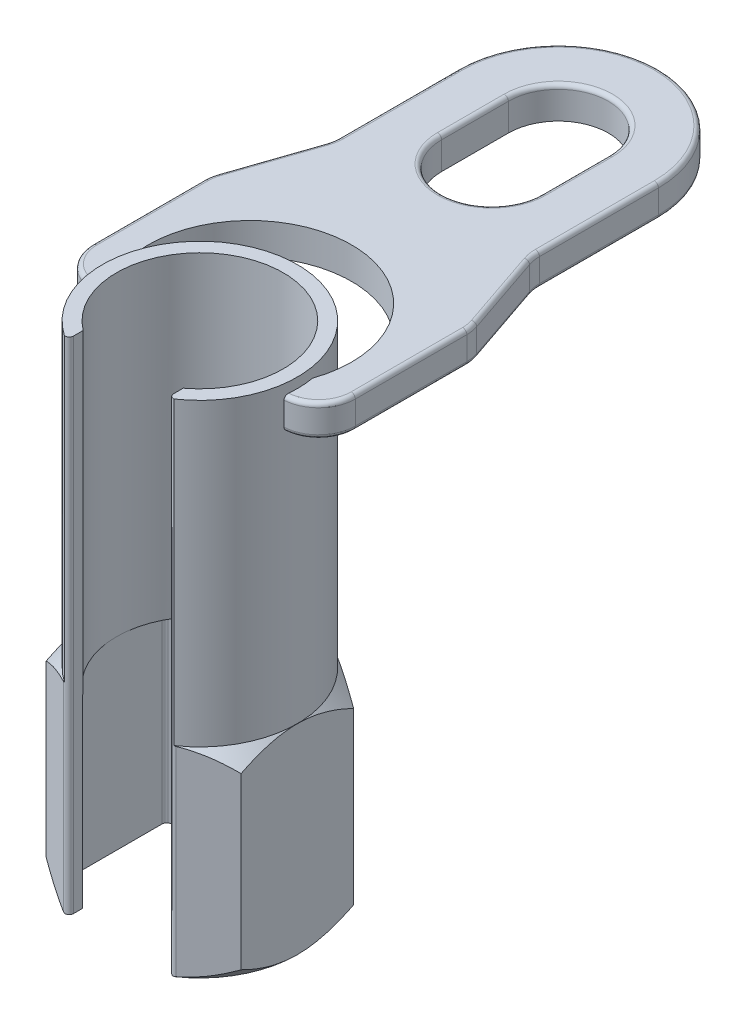
SolidWorks part; units mm, degrees
ref_plane "Front" through (0, 0, 0) normal (0, 0, 1) x (1, 0, 0)
ref_plane "Top" through (0, 0, 0) normal (0, 1, 0) x (1, 0, 0)
ref_plane "Right" through (0, 0, 0) normal (1, 0, 0) x (0, 0, -1)
sketch "Sketch1" plane through (0, 0, 0) normal (0, 1, 0) x (1, 0, 0)
  line L0 (-6, -8) -> (-6, -10.0359)
  line L1 (0, 13.5) -> (-11.6913, 6.75)
  line L2 (0, 11.9615) -> (0, -7.933) construction
  line L3 (-11.6913, 6.75) -> (-11.6913, -6.75)
  line L4 (-11.6913, -6.75) -> (-6, -10.0359)
  line L5 (6, -10.0359) -> (11.6913, -6.75)
  line L6 (11.6913, -6.75) -> (11.6913, 6.75)
  line L7 (11.6913, 6.75) -> (0, 13.5)
  line L8 (6, -8) -> (6, -10.0359)
  arc A0 (6, -10.0343) -> (-6, -10.0343) centre (0, 0) ccw construction
  arc A1 (6, -8) -> (-6, -8) centre (0, 0) ccw
  point P18 (-11.6913, -6.75)
  point P26 (11.6913, 6.75)
  dimension "D" = 27
  dimension "D2" = 20
  dimension "C" = 12
extrude "Extrude1" add sketch "Sketch1" along normal blind 24
sketch "Sketch3" plane through (0, 24, 0) normal (0, 1, 0) x (-1, 0, 0)
  line L0 (-11.6913, 6.75) -> (-11.6913, -6.75) construction
  line L2 (-6, 10.0342) -> (-6, 8)
  line L3 (6, 10.0342) -> (6, 8)
  arc A0 (-6, 8) -> (6, 8) centre (0, 0) ccw
  arc A1 (-6, 8) -> (6, 8) centre (0, 0) ccw construction
  arc A2 (-6, 10.0342) -> (6, 10.0342) centre (0, 0) ccw
  dimension "D1" = 0.0001
extrude "Extrude2" add sketch "Sketch3" along normal blind 36
sketch "Sketch8" plane through (0, 0, 0) normal (0, -1, 0) x (1, 0, 0)
  line L1 (11.6913, 6.75) -> (11.6913, -6.75) construction
  circle A0 centre (0, 0) radius 11.6913
extrude "Cut-Extrude4" cut sketch "Sketch8" against normal through all draft 45 flip side to cut
sketch "Sketch19" plane through (0, 24, 0) normal (0, 1, 0) x (-1, 0, 0)
  circle A1 centre (0, 0) radius 11.6912
  arc A2 (-6, 10.0342) -> (6, 10.0342) centre (0, 0) ccw construction
extrude "Cut-Extrude6" cut sketch "Sketch19" against normal through all draft 45 flip side to cut
sketch "Sketch26" plane through (0, 0, 0) normal (0, -1, 0) x (1, 0, 0)
  line L1 (-10, -5.7735) -> (0, -11.547)
  line L2 (0, -11.547) -> (10, -5.7735)
  line L3 (10, -5.7735) -> (10, 5.7735)
  line L4 (10, 5.7735) -> (0, 11.547)
  line L5 (0, 11.547) -> (-10, 5.7735)
  line L6 (-10, 5.7735) -> (-10, -5.7735)
  circle A0 centre (0, 0) radius 10 construction
  dimension "D1" = 20
extrude "Cut-Extrude9" cut sketch "Sketch26" against normal up to vertex (22.1912 mm away)
fillet "Fillet1" radius 0.5 7 edges at (-10, 11.0956, -5.7735) (-10, 11.0956, 5.7735) (10, 11.0956, 5.7735) (10, 11.0956, -5.7735) (-6, 12, 10.0359) (6, 12, 10.0359) (0, 11.0956, -11.547)
sketch "Sketch4" [suppressed] plane through (0, 0, 0) normal (0, 1, 0) x (-1, 0, 0)
  line L0 (0, -11.2014) -> (0, 12.8888) construction
  line L1 (-10, -2.5) -> (10, -2.5)
  line L2 (-10, -2.5) -> (-10, 3.8)
  line L3 (-10, 3.8) -> (10, 3.8)
  line L4 (10, -2.5) -> (10, 3.8)
  line L5 (16.2585, 0) -> (-21.4153, 0) construction
  dimension "D1" = 20
  dimension "D2" = 3.8
  dimension "D3" = 2.5
sketch "Sketch12" [suppressed] plane through (0, 0, 0) normal (0, 1, 0) x (1, 0, 0)
  line L0 (-11, -4) -> (11, -4)
  line L1 (0, 0) -> (-11.4274, 0) construction
  line L2 (-11, 2.7) -> (11, 2.7)
  line L3 (-4.5, 14.3091) -> (4.5, 14.3091)
  line L4 (-7, 3.2909) -> (-7, -3.2909) construction
  line L5 (7, -3.2909) -> (7, 3.2909) construction
  arc A0 (-11, -4) -> (11, -4) centre (0, 0) ccw
  arc A1 (-6.3246, -3) -> (6.3246, -3) centre (0, 0) ccw construction
  arc A2 (-4.5, 14.3091) -> (-11, 2.7) centre (2.617, 2.7) ccw
  arc A3 (-4.5, 14.3091) -> (4.5, 14.3091) centre (0, 0) ccw construction
  arc A4 (4.5, 14.3091) -> (11, 2.7) centre (-2.617, 2.7) cw
ref_plane "Plane3" through (0, 55, 0) normal (0, 1, 0) x (-1, 0, 0)
sketch "Sketch16" plane through (0, 55, 0) normal (0, 1, 0) x (-1, 0, 0)
  line L5 (0, 0) -> (0, 54.2988) construction
  line L6 (-12, -43) -> (-12, -28.7294)
  line L10 (12, -28.7294) -> (12, -43)
  line L11 (15.5146, -17.6904) -> (12.2354, -27.3096)
  line L12 (-15.5146, -17.6904) -> (-12.2354, -27.3096)
  line L13 (-15.75, -2.8932) -> (-15.75, -16.2706)
  line L14 (15.75, -2.8932) -> (15.75, -16.2706)
  line L15 (38.3763, 1.5) -> (-38.1367, 1.5) construction
  arc A0 (-6.5807, 9.6633) -> (6.5807, 9.6633) centre (0, 0) ccw construction
  arc A1 (-11.5946, 1.5) -> (11.5946, 1.5) centre (0, 0) ccw
  arc A2 (15.75, -2.8932) -> (11.5946, 1.5) centre (11.35, -2.8932) ccw
  arc A3 (-15.75, -2.8932) -> (-11.5946, 1.5) centre (-11.35, -2.8932) cw
  arc A4 (-15.75, -16.2706) -> (-15.5146, -17.6904) centre (-11.35, -16.2706) ccw
  arc A5 (-12.2354, -27.3096) -> (-12, -28.7294) centre (-16.4, -28.7294) cw
  arc A7 (15.75, -16.2706) -> (15.5146, -17.6904) centre (11.35, -16.2706) cw
  arc A8 (12.2354, -27.3096) -> (12, -28.7294) centre (16.4, -28.7294) ccw
  arc A15 (12, -43) -> (-12, -43) centre (0, -43) cw
  point P18 (-15.75, -17)
  point P22 (-12, -28)
  point P25 (15.75, -17)
  point P30 (12, -28)
  dimension "D1" = 31.5
  dimension "D2" = 17
  dimension "D3" = 28
  dimension "D4" = 4.4
  dimension "D6" = 24
  dimension "D7" = 43
  dimension "D14" = 1.5
extrude "Extrude7" add sketch "Sketch16" along normal blind 3.8
sketch "Sketch25" plane through (0, 58.8, 0) normal (0, -1, 0) x (1, 0, 0)
  line L1 (-29.4486, 0) -> (37.9585, 0) construction
  line L3 (0, -57.3769) -> (0, 10.8445) construction
  line L4 (-6, -43) -> (-6, -35)
  line L5 (6, -43) -> (6, -35)
  arc A0 (-6.5807, 9.6633) -> (6.5807, 9.6633) centre (0, 0) ccw construction
  arc A2 (-12, -43) -> (12, -43) centre (0, -43) ccw construction
  arc A6 (11.5189, -2) -> (-11.5189, -2) centre (0, 0) cw
  arc A7 (11.5189, -2) -> (-11.5189, -2) centre (0, -6) cw
  arc A8 (6, -43) -> (-6, -43) centre (0, -43) cw
  arc A9 (6, -35) -> (-6, -35) centre (0, -35) ccw
  dimension "D1" = 20
  dimension "D2" = 12
  dimension "D3" = 2
  dimension "D4" = 6
extrude "Cut-Extrude8" cut sketch "Sketch25" along normal up to next
fillet "Fillet4" radius 0.5 30 edges at (6, 58.8, -39) (0, 58.8, -49) (-6, 58.8, -39) (14.5466, 58.8, 0.1304) (15.75, 58.8, -9.5819) (15.6908, 58.8, -16.9902) (-14.5466, 58.8, 0.1304) (-15.75, 58.8, -9.5819) (-15.6908, 58.8, -16.9902) (-13.875, 58.8, -22.5) (-12.0592, 58.8, -28.0098) (-12, 58.8, -35.8647) (0, 58.8, -55) (12, 58.8, -35.8647) (12.0592, 58.8, -28.0098) (14.5466, 55, 0.1304) (15.75, 55, -9.5819) (15.6908, 55, -16.9902) (-14.5466, 55, 0.1304) (-15.75, 55, -9.5819) (-15.6908, 55, -16.9902) (-13.875, 55, -22.5) (-12.0592, 55, -28.0098) (-12, 55, -35.8647) (0, 55, -55) (12, 55, -35.8647) (12.0592, 55, -28.0098) (0, 58.8, -29) (13.875, 58.8, -22.5) (13.875, 55, -22.5)
sketch "Sketch20" [suppressed] plane through (0, 0, 0) normal (0, 1, 0) x (1, 0, 0)
  line L0 (0, 0) -> (0, 12.8849) construction
  line L1 (-7.5, -9.3675) -> (-7.5, -14.4157)
  line L2 (7.5, -9.3675) -> (7.5, -14.4157)
  arc A0 (7.5, -14.4157) -> (-7.5, -14.4157) centre (0, 0) ccw
  arc A1 (7.5, -9.3675) -> (-7.5, -9.3675) centre (0, 0) ccw
  circle A2 centre (0, 0) radius 16.25 construction
  circle A3 centre (0, 0) radius 12 construction
  dimension "D1" = 27
  dimension "D2" = 20
  dimension "D3" = 12
extrude "Extrude3" [suppressed] add sketch "Sketch20" along normal blind 38
ref_plane "Plane7" [suppressed] through (0, 41.999, 0) normal (0, 1, 0) x (-1, 0, 0)
sketch "Sketch21" [suppressed] plane through (0, 41.999, 0) normal (0, 1, 0) x (-1, 0, 0)
  line L1 (2.5, 16.0565) -> (2.5, 19.8734)
  line L2 (7.5, 14.4157) -> (7.5, 9.3675) construction
  line L4 (7.5, 14.4157) -> (7.5, 18.5729)
  arc A1 (2.5, 16.0565) -> (7.5, 14.4157) centre (0, 0) ccw
  arc A2 (2.5, 19.8734) -> (7.5, 18.5729) centre (0, 0) ccw
  arc A3 (-7.5, 14.4157) -> (7.5, 14.4157) centre (0, 0) ccw construction
  dimension "D1" = 3.42
  dimension "D2" = 2.5
extrude "Extrude4" [suppressed] add sketch "Sketch21" against normal blind 12 separate body
ref_plane "Plane6" [suppressed] through (5.0421, 41.999, -19.385) normal (0.2517, 0, -0.9678) x (-0.9678, 0, -0.2517)
sketch "Sketch22" [suppressed] plane through (5.0421, 41.999, -19.385) normal (0.2517, 0, -0.9678) x (-0.9678, 0, -0.2517)
  line L0 (20.03, 0) -> (-20.03, 0) construction
  line L1 (0, 0) -> (0, 14.8678) construction
  line L2 (-3.2, -3.3) -> (3.2, -3.3)
  line L3 (-3.2, -3.3) -> (-3.2, -9.7)
  line L4 (-3.2, -9.7) -> (3.2, -9.7)
  line L5 (3.2, -3.3) -> (3.2, -9.7)
  line L7 (-18.9345, -6.5) -> (19.4735, -6.5) construction
  dimension "D1" = 5.6
  dimension "D2" = 6
  dimension "D3" = 5.6
extrude "Extrude5" [suppressed] add sketch "Sketch22" along normal blind 10 and the other way up to next
sketch "Sketch23" [suppressed] plane through (8.0628, 0, -30.9986) normal (0.2517, 0, -0.9678) x (-0.9678, 0, -0.2517)
  circle A0 centre (0, 35.499) radius 4.5255
extrude "Extrude6" [suppressed] add sketch "Sketch23" along normal blind 28 draft 2
dome "Dome1" [suppressed] faces to dome 1 distance 3 parameters "D1"=3
sketch "Sketch24" [suppressed] plane through (0, 0, 0) normal (0, -1, 0) x (1, 0, 0)
  line L2 (-12, 6.9282) -> (-12, -6.9282)
  line L3 (-12, -6.9282) -> (0, -13.8564)
  line L4 (0, -13.8564) -> (12, -6.9282)
  line L5 (12, -6.9282) -> (12, 6.9282)
  line L6 (12, 6.9282) -> (0, 13.8564)
  line L7 (0, 13.8564) -> (-12, 6.9282)
  circle A0 centre (0, 0) radius 12 construction
  dimension "D1" = 20
extrude "Cut-Extrude7" [suppressed] cut sketch "Sketch24" against normal through all
fillet "Fillet2" [suppressed] radius 0.5
fillet "Fillet3" [suppressed] radius 0.5
fillet "Fillet5" [suppressed] radius 1
